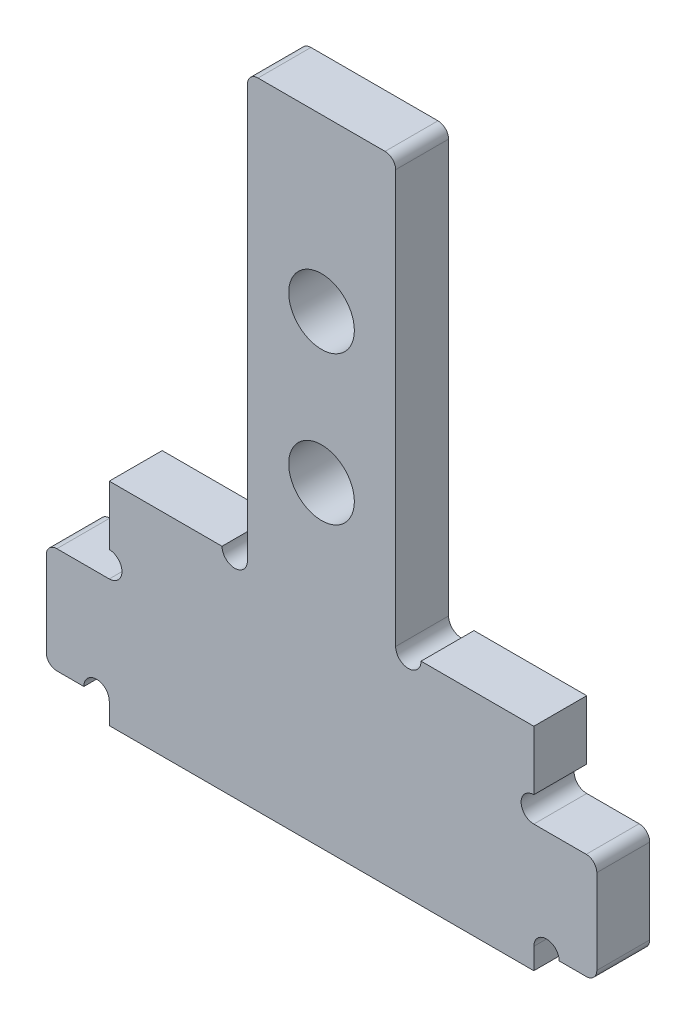
SolidWorks part; units mm, degrees
ref_plane "前视基准面" through (0, 0, 0) normal (0, 0, 1) x (1, 0, 0)
ref_plane "上视基准面" through (0, 0, 0) normal (0, 1, 0) x (1, 0, 0)
ref_plane "右视基准面" through (0, 0, 0) normal (1, 0, 0) x (0, 0, -1)
sketch "草图1" plane through (0, 0, 0) normal (0, 0, 1) x (1, 0, 0)
  line L0 (-10.025, 6) -> (-13, 6)
  line L1 (-13, 6) -> (-13, 1)
  line L2 (-13, 1) -> (-10.025, 1)
  line L3 (-10.025, 1) -> (-10.025, 0)
  line L4 (-10.025, 0) -> (10.025, 0)
  line L5 (10.025, 0) -> (10.025, 1)
  line L6 (10.025, 1) -> (13, 1)
  line L7 (13, 1) -> (13, 6)
  line L8 (13, 6) -> (10.025, 6)
  line L9 (10.025, 6) -> (10.025, 10)
  line L10 (10.025, 10) -> (3.5, 10)
  line L11 (3.5, 10) -> (3.5, 30)
  line L12 (3.5, 30) -> (-3.5, 30)
  line L13 (-3.5, 30) -> (-3.5, 10)
  line L14 (-3.5, 10) -> (-10.025, 10)
  line L15 (-10.025, 10) -> (-10.025, 6)
  point P10 (0, 0)
  point P17 (-13, 3.5)
  dimension "D1" = 20.05
  dimension "D2" = 26
  dimension "D3" = 5
  dimension "D4" = 6.5
  dimension "D5" = 1
  dimension "D6" = 20
  dimension "D7" = 7
extrude "凸台-拉伸1" add sketch "草图1" along normal mid plane 2.5
sketch "草图2" plane through (0, 0, 1.25) normal (0, 0, 1) x (1, 0, 0)
  line L0 (-10.025, 10) -> (-10.025, 6) construction
  line L1 (-13, 1) -> (-10.025, 1) construction
  line L2 (10.025, 6) -> (10.025, 10) construction
  line L4 (-3.5, 10) -> (-10.025, 10) construction
  line L5 (10.025, 10) -> (3.5, 10) construction
  line L7 (10.025, 1) -> (13, 1) construction
  circle A0 centre (-10.025, 6.6) radius 0.6
  circle A1 centre (-10.625, 1) radius 0.6
  circle A2 centre (10.025, 6.6) radius 0.6
  circle A3 centre (10.625, 1) radius 0.6
  circle A4 centre (-4.1, 10) radius 0.6
  circle A5 centre (4.1, 10) radius 0.6
  point P7 (0, 0)
  point P17 (10.625, 1)
  point P31 (-10.625, 1)
  dimension "D1" = 1.2
extrude "切除-拉伸1" cut sketch "草图2" against normal through all
fillet "圆角1" radius 0.5 6 edges at (13, 1, 0) (13, 6, 0) (-13, 1, 0) (-13, 6, 0) (3.5, 30, 0) (-3.5, 30, 0)
sketch "草图3" plane through (0, 0, 1.25) normal (0, 0, 1) x (1, 0, 0)
  line L0 (0, 21.95) -> (0, 14.95) construction
  line L1 (10.025, 10) -> (4.7, 10) construction
  circle A0 centre (0, 14.95) radius 1.55
  circle A1 centre (0, 21.95) radius 1.55
  point P4 (0, 23.5589)
  dimension "D1" = 7
  dimension "D2" = 3.1
  dimension "D3" = 4.95
extrude "切除-拉伸2" cut sketch "草图3" against normal through all
